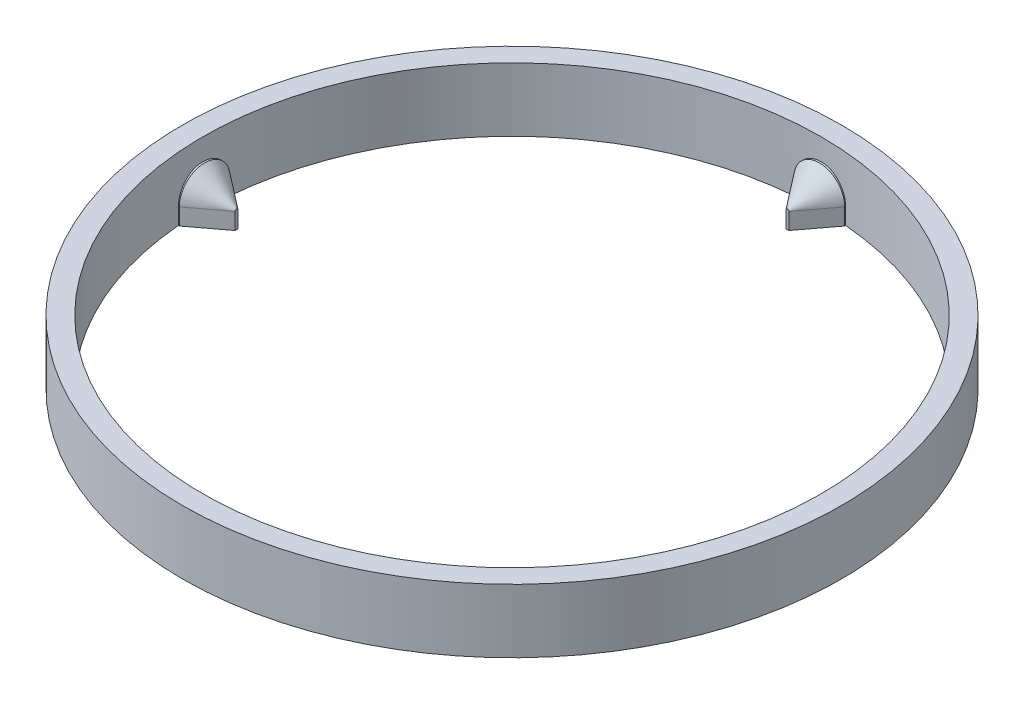
SolidWorks part; units mm, degrees
ref_plane "前视基准面" through (0, 0, 0) normal (0, 0, 1) x (1, 0, 0)
ref_plane "上视基准面" through (0, 0, 0) normal (0, 1, 0) x (1, 0, 0)
ref_plane "右视基准面" through (0, 0, 0) normal (1, 0, 0) x (0, 0, -1)
sketch "草图1" plane through (0, 0, 0) normal (0, 1, 0) x (1, 0, 0)
  circle A0 centre (0, 0) radius 48.6
  circle A2 centre (0, 0) radius 51.8
  circle A3 centre (0, 0) radius 51.8 construction
  arc A4 (-3.8505, -48.1463) -> (46.5761, -12.7889) centre (0, 0) ccw construction
  dimension "D1" = 0.3
extrude "凸台-拉伸1" add sketch "草图1" along normal up to surface (10 mm away)
sketch "草图2" plane through (0, 0, 0) normal (0, 0, 1) x (1, 0, 0)
  line L3 (0, 0) -> (0, 10) construction
  line L5 (-4, 2.6) -> (-4, 0)
  line L6 (-4, 0) -> (4, 0)
  line L7 (-11.2889, 0) -> (0, 0)
  line L8 (-11.2889, 10) -> (-11.2889, 0)
  line L9 (-4.7889, 10) -> (-11.2889, 10)
  line L10 (-4.7889, 6.4) -> (-4.7889, 10)
  line L11 (-1.7889, 6.4) -> (-4.7889, 6.4)
  line L12 (4.2, 0) -> (4.2, 2.6)
  line L13 (0, 0) -> (4.2, 0)
  line L14 (-11.2889, 0) -> (0, 0)
  line L15 (-11.2889, 10) -> (-11.2889, 0)
  line L16 (-4.7889, 10) -> (-11.2889, 10)
  line L17 (-4.7889, 6.4) -> (-4.7889, 10)
  line L18 (-1.7889, 6.4) -> (-4.7889, 6.4)
  line L19 (4.2, 0) -> (4.2, 2.6)
  line L20 (0, 0) -> (4.2, 0)
  line L21 (4, 2.6) -> (4, 0)
  line L22 (-4, 2.6) -> (4, 0) construction
  line L23 (-4, 0) -> (4, 2.6) construction
  arc A1 (4.2, 2.6) -> (-1.7889, 6.4) centre (0, 2.6) ccw
  arc A2 (4.2, 2.6) -> (-1.7889, 6.4) centre (0, 2.6) ccw
  arc A3 (4, 2.6) -> (-4, 2.6) centre (0, 2.6) ccw
  point P4 (0, 1.3)
  dimension "D2" = 0.2
  dimension "D1" = 0
extrude "凸台-拉伸4" add sketch "草图2" along normal up to body from vertex separate body contours L21 A3 L5 L6
chamfer "倒角1" distance 5 angle 37 2 edges at (0, 6.6, 43.2999) (4, 1.3, 43.2999)
pattern_circular "阵列(圆周)4" count 4 over 360 about axis through (0, 0, 0) along (0, 1, 0) of "凸台-拉伸4", "倒角1"
